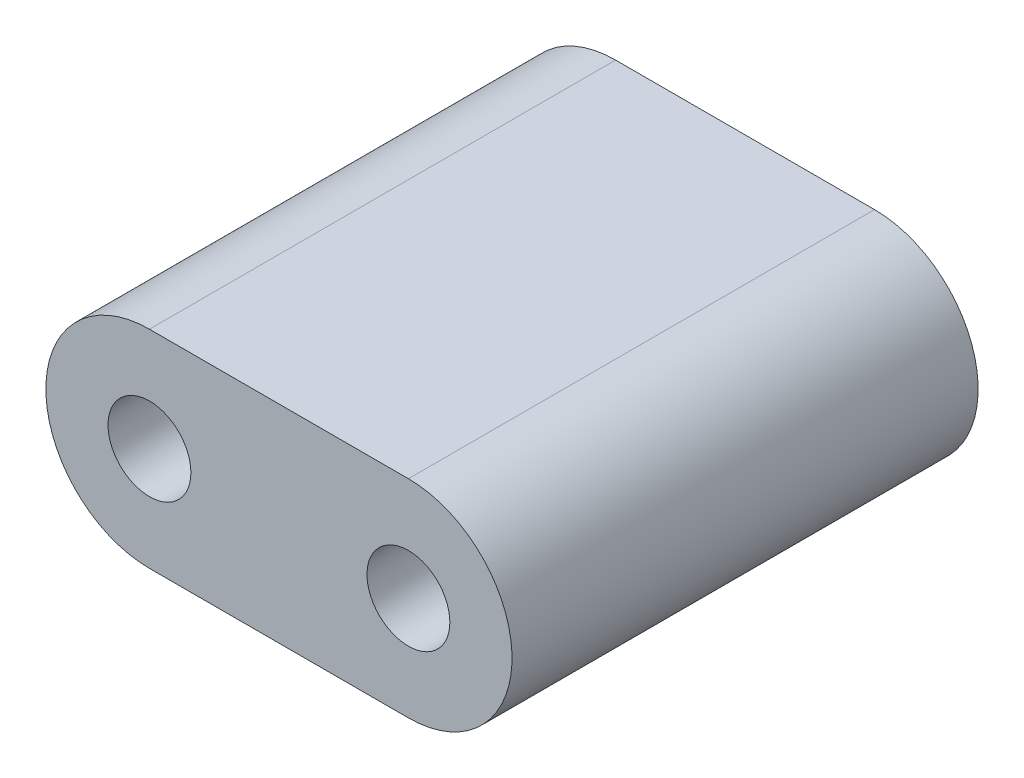
SolidWorks part; units mm, degrees
ref_plane "Front Plane" through (0, 0, 0) normal (0, 0, 1) x (1, 0, 0)
ref_plane "Top Plane" through (0, 0, 0) normal (0, 1, 0) x (1, 0, 0)
ref_plane "Right Plane" through (0, 0, 0) normal (1, 0, 0) x (0, 0, -1)
sketch "Sketch1" plane through (0, 0, 0) normal (0, 0, 1) x (1, 0, 0)
  line L0 (-5, 0) -> (5, 0) construction
  line L1 (-5, 4) -> (5, 4)
  line L2 (-5, -4) -> (5, -4)
  arc A0 (-5, 4) -> (-5, -4) centre (-5, 0) ccw
  arc A1 (5, -4) -> (5, 4) centre (5, 0) ccw
  circle A2 centre (-5, 0) radius 1.6
  circle A3 centre (5, 0) radius 1.6
  point P2 (0, 0)
  dimension "D3" = 3.2
  dimension "D1" = 10
  dimension "D2" = 8
extrude "Boss-Extrude1" add sketch "Sketch1" along normal blind 18
